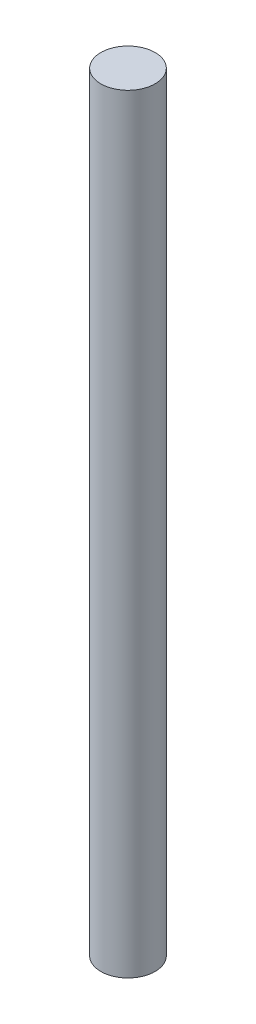
SolidWorks part; units mm, degrees
ref_plane "Front Plane" through (0, 0, 0) normal (0, 0, 1) x (1, 0, 0)
ref_plane "Top Plane" through (0, 0, 0) normal (0, 1, 0) x (1, 0, 0)
ref_plane "Right Plane" through (0, 0, 0) normal (1, 0, 0) x (0, 0, -1)
sketch "Sketch1" plane through (0, 0, 0) normal (0, 1, 0) x (1, 0, 0)
  circle A0 centre (0, 0) radius 1.5
  dimension "D1" = 3
extrude "Boss-Extrude1" add sketch "Sketch1" along normal blind 42.5
